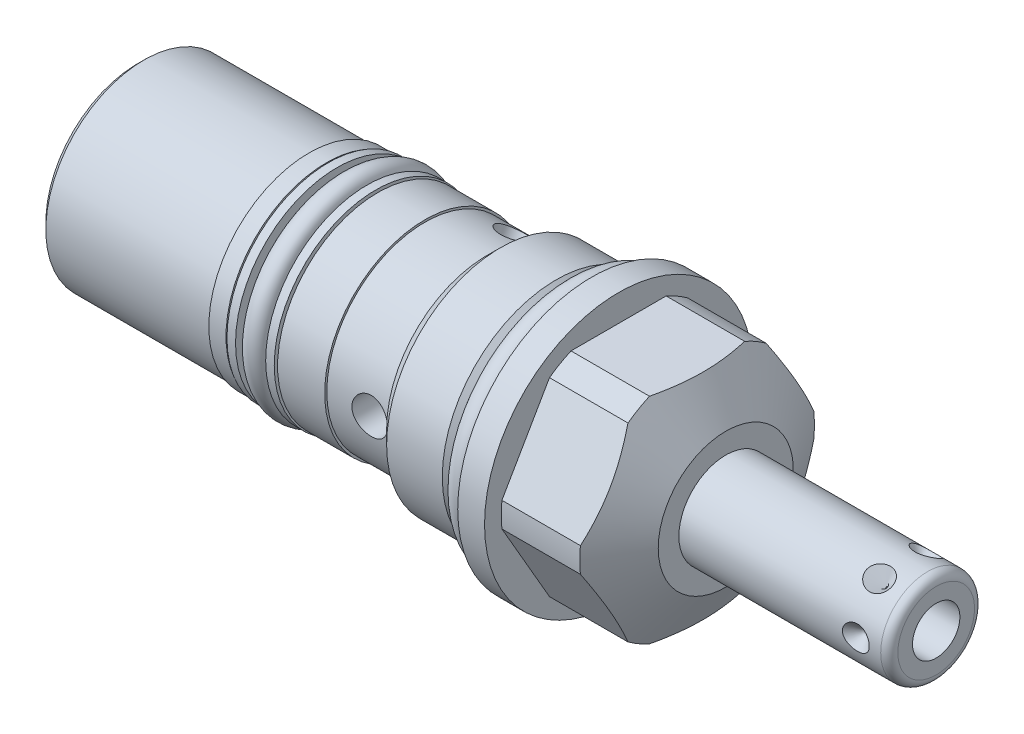
SolidWorks part; units mm, degrees
material "Alloy Steel"
ref_plane "Front Plane" through (0, 0, 0) normal (0, 0, 1) x (1, 0, 0)
ref_plane "Top Plane" through (0, 0, 0) normal (0, 1, 0) x (1, 0, 0)
ref_plane "Right Plane" through (0, 0, 0) normal (1, 0, 0) x (0, 0, -1)
sketch "Sketch1" plane through (0, 0, 0) normal (0, 0, 1) x (1, 0, 0)
  line L0 (0, 0) -> (113.8544, 0) construction
  line L1 (0, 15.875) -> (3.175, 15.875)
  line L2 (3.175, 15.875) -> (3.175, 13.8938)
  line L3 (3.175, 13.8938) -> (12.4728, 13.8938)
  line L4 (12.4728, 13.8938) -> (15.875, 8.001)
  line L5 (15.875, 8.001) -> (15.875, 0)
  line L6 (15.875, 0) -> (-53.7972, 0)
  line L7 (-53.7972, 0) -> (-53.7972, 11.6205)
  line L8 (0, 15.875) -> (0, 12.0015)
  line L9 (0, 12.0015) -> (-2.7178, 12.0015)
  line L10 (-2.7178, 12.0015) -> (-4.21, 13.4937)
  line L11 (-4.21, 13.4937) -> (-10.8013, 13.4937)
  line L12 (-10.8013, 13.4937) -> (-12.4206, 11.8745)
  line L14 (-12.4206, 11.8745) -> (-12.4206, 11.6205)
  line L15 (-12.4206, 11.6205) -> (-53.7972, 11.6205)
  dimension "D1" = 31.75
  dimension "D2" = 16.002
  dimension "D3" = 3.175
  dimension "D4" = 15.875
  dimension "D5" = 27.7876
  dimension "D6" = 30
  dimension "D7" = 53.7972
  dimension "D8" = 51.0794
  dimension "D9" = 24.003
  dimension "D10" = 45
  dimension "D11" = 26.9875
  dimension "D12" = 9.7028
  dimension "D13" = 23.749
  dimension "D14" = 23.241
revolve "Revolve1" add sketch "Sketch1" angle 360 about L0
sketch "Sketch2" plane through (15.875, 0, 0) normal (1, 0, 0) x (0, 0, -1)
  line L1 (7.3323, 12.7) -> (-7.3323, 12.7)
  line L2 (-7.3323, 12.7) -> (-14.6647, 0)
  line L3 (-14.6647, 0) -> (-7.3323, -12.7)
  line L4 (-7.3323, -12.7) -> (7.3323, -12.7)
  line L5 (7.3323, -12.7) -> (14.6647, 0)
  line L6 (14.6647, 0) -> (7.3323, 12.7)
  circle A0 centre (0, 0) radius 12.7 construction
  dimension "D1" = 25.4
extrude "Cut-Extrude1" cut sketch "Sketch2" against normal up to surface (12.7 mm away) flip side to cut up to face at (3.175, 0, 15.875)
sketch "Sketch3" plane through (0, 0, 0) normal (0, 0, 1) x (1, 0, 0)
  line L0 (0, 0) -> (52.5154, 0) construction
  line L1 (15.875, 5.5563) -> (39.7764, 5.5562)
  line L2 (15.875, -8.001) -> (15.875, 8.001) construction
  line L3 (40.7924, 4.5402) -> (40.7924, 0)
  line L4 (40.7924, 0) -> (15.875, 0)
  line L5 (15.875, 0) -> (15.875, 5.5563)
  line L6 (0, 15.875) -> (0, -15.875) construction
  arc A0 (40.7924, 4.5402) -> (39.7764, 5.5562) centre (39.7764, 4.5402) ccw
  dimension "D1" = 1.016
  dimension "D2" = 40.7924
  dimension "D3" = 11.1125
revolve "Revolve2" add sketch "Sketch3" angle 360 about L0
sketch "Sketch4" plane through (0, 0, 0) normal (0, 1, 0) x (1, 0, 0)
  line L0 (36.83, 10.0738) -> (36.83, 0) construction
  line L1 (40.7924, -4.5402) -> (40.7924, 4.5402) construction
  line L2 (38.4175, 5.5563) -> (36.83, 5.5563)
  line L3 (39.7764, 5.5563) -> (15.875, 5.5563) construction
  line L4 (36.83, 5.5563) -> (36.83, 3.9687)
  line L5 (36.83, 3.9687) -> (38.4175, 5.5563)
  dimension "D1" = 3.9624
  dimension "D2" = 45
  dimension "D3" = 3.175
revolve "Cut-Revolve1" cut sketch "Sketch4" angle 360 about L0
pattern_circular "CirPattern1" count 6 over 360 about axis through (0, 0, 0) along (-1, 0, 0) of "Cut-Revolve1"
sketch "Sketch5" plane through (0, 0, 0) normal (0, 0, 1) x (1, 0, 0)
  line L0 (0, 0) -> (44.9273, 0) construction
  line L1 (40.7924, 2.8067) -> (30.6324, 2.8067)
  line L2 (40.7924, -4.5402) -> (40.7924, 4.5402) construction
  line L3 (30.6324, 2.8067) -> (28.946, 0)
  line L4 (28.946, 0) -> (40.7924, 0)
  line L5 (40.7924, 0) -> (40.7924, 2.8067)
  dimension "D1" = 10.16
  dimension "D2" = 59
  dimension "D3" = 5.6134
revolve "Cut-Revolve2" cut sketch "Sketch5" angle 360 about L0
sketch "Sketch6" plane through (0, 0, 0) normal (0, 0, 1) x (1, 0, 0)
  line L0 (-19.7612, 11.6205) -> (-19.7612, 11.8745)
  line L1 (-12.4206, 11.6205) -> (-53.7972, 11.6205) construction
  line L2 (-19.7612, 11.8745) -> (-33.4772, 11.8745)
  line L3 (-33.4772, 11.8745) -> (-33.4772, 11.6205)
  line L4 (-33.4772, 11.6205) -> (-19.7612, 11.6205)
  line L5 (0, 0) -> (-62.9111, 0) construction
  line L6 (-53.7972, 11.6205) -> (-53.7972, -11.6205) construction
  dimension "D1" = 13.716
  dimension "D2" = 23.749
  dimension "D3" = 20.32
revolve "Revolve3" add sketch "Sketch6" angle 360 about L5
sketch "Sketch7" plane through (-53.7972, 0, 0) normal (-1, 0, 0) x (0, 0, 1)
  circle A0 centre (0, 0) radius 0.8001
  dimension "D1" = 1.6002
extrude "Cut-Extrude2" cut sketch "Sketch7" against normal blind 0.762
sketch "Sketch8" plane through (0, 0, 0) normal (0, 0, 1) x (1, 0, 0)
  line L0 (0, 0) -> (-56.7277, 0) construction
  line L1 (-19.7612, 11.8745) -> (-33.4772, 11.8745) construction
  line L2 (-31.4452, 11.8745) -> (-25.3365, 11.8745)
  line L3 (-31.4452, 11.8745) -> (-31.4452, 9.8298)
  line L4 (-31.4452, 9.8298) -> (-25.3365, 9.8298)
  line L5 (-25.3365, 11.8745) -> (-25.3365, 9.8298)
  line L6 (-53.7972, 11.6205) -> (-53.7972, -11.6205) construction
  dimension "D1" = 6.1087
  dimension "D2" = 22.352
  dimension "D3" = 19.6596
revolve "Cut-Revolve3" cut sketch "Sketch8" angle 360 about L0
sketch "Sketch9" plane through (0, 0, 0) normal (0, 0, 1) x (1, 0, 0)
  line L0 (0, 0) -> (-59.2046, 0) construction
  line L1 (-28.3908, 14.9069) -> (-28.3908, -14.8344) construction
  line L2 (-31.4452, -11.8745) -> (-31.4452, 11.8745) construction
  line L3 (-25.3365, 9.8298) -> (-25.3365, -9.8298) construction
  line L4 (-25.3365, 9.8298) -> (-31.4452, 9.8298) construction
  line L5 (-26.6065, 12.0142) -> (-25.5905, 12.0142)
  line L6 (-26.6065, 12.0142) -> (-26.6065, 9.8298)
  line L7 (-26.6065, 9.8298) -> (-25.5905, 9.8298)
  line L8 (-25.5905, 12.0142) -> (-25.5905, 9.8298)
  line L9 (-25.3365, 11.8745) -> (-25.3365, -11.8745) construction
  line L10 (-31.1912, 12.0142) -> (-31.1912, 9.8298)
  line L11 (-30.1752, 9.8298) -> (-31.1912, 9.8298)
  line L12 (-30.1752, 12.0142) -> (-30.1752, 9.8298)
  line L13 (-30.1752, 12.0142) -> (-31.1912, 12.0142)
  dimension "D1" = 1.016
  dimension "D2" = 0.254
  dimension "D3" = 2.1844
revolve "Revolve4" add sketch "Sketch9" angle 360 about L0
sketch "Sketch10" plane through (0, 0, 0) normal (0, 1, 0) x (1, 0, 0)
  line L0 (-14.6812, 23.0369) -> (-14.6812, -3.4735) construction
  line L1 (-53.7972, 11.6205) -> (-53.7972, -11.6205) construction
  line L2 (-14.6812, -11.6205) -> (-16.7894, -11.6205)
  line L4 (-16.7894, -11.6205) -> (-16.7894, -0.7937)
  line L5 (-16.7894, -0.7937) -> (-14.6812, -0.7937)
  line L6 (-14.6812, -0.7937) -> (-14.6812, -11.6205)
  line L7 (-19.7612, -11.6205) -> (-12.4206, -11.6205) construction
  dimension "D1" = 39.116
  dimension "D2" = 4.2164
  dimension "D3" = 0.7937
revolve "Cut-Revolve4" cut sketch "Sketch10" angle 360 about L0
pattern_circular "CirPattern2" count 3 over 360 about axis through (0, 0, 0) along (1, 0, 0) of "Cut-Revolve4"
chamfer "Chamfer1" distance 0.762 angle 45 1 edges at (-53.7972, 0, 11.6205)
sketch "Sketch11" plane through (0, 0, 0) normal (0, 0, 1) x (1, 0, 0)
  line L0 (0, 0) -> (23.6366, 0) construction
  line L1 (0, 15.875) -> (0, -15.875) construction
  line L2 (0, 12.0015) -> (-2.7178, 12.0015) construction
  circle A0 centre (-1.4732, 13.4747) radius 1.4732
  dimension "D1" = 2.9464
  dimension "D2" = 26.9494
revolve "Revolve5" add sketch "Sketch11" angle 360 about L0
sketch "Sketch12" plane through (0, 0, 0) normal (0, 0, 1) x (1, 0, 0)
  line L0 (0, 0) -> (-56.0967, 0) construction
  line L1 (-26.6065, 9.8298) -> (-30.1752, 9.8298) construction
  line L2 (-28.3908, 11.1379) -> (-28.3908, 6.0377) construction
  line L3 (-31.4452, -11.8745) -> (-31.4452, 11.8745) construction
  line L4 (-25.3365, 9.8298) -> (-25.3365, -9.8298) construction
  circle A0 centre (-28.3908, 11.1379) radius 1.3081
  dimension "D1" = 2.6162
revolve "Revolve7" add sketch "Sketch12" angle 360 about L0
sketch "Sketch13" plane through (0, 0, 0) normal (0, 0, 1) x (1, 0, 0)
  line L0 (-63.2754, 0) -> (0, 0) construction
  line L1 (-53.7972, 4.572) -> (-51.7144, 4.1293)
  line L2 (-53.7972, 10.8585) -> (-53.7972, -10.8585) construction
  line L3 (-51.7144, 4.1293) -> (-51.0395, 3.4544)
  line L4 (-51.0395, 3.4544) -> (-42.0116, 3.4544)
  line L5 (-42.0116, 3.4544) -> (-42.0116, 0)
  line L6 (-42.0116, 0) -> (-53.7972, 0)
  line L7 (-53.7972, 0) -> (-53.7972, 4.572)
  dimension "D1" = 12
  dimension "D2" = 9.144
  dimension "D3" = 45
  dimension "D4" = 2.0828
  dimension "D5" = 6.9088
  dimension "D6" = 11.7856
revolve "Cut-Revolve5" cut sketch "Sketch13" angle 360 about L0
